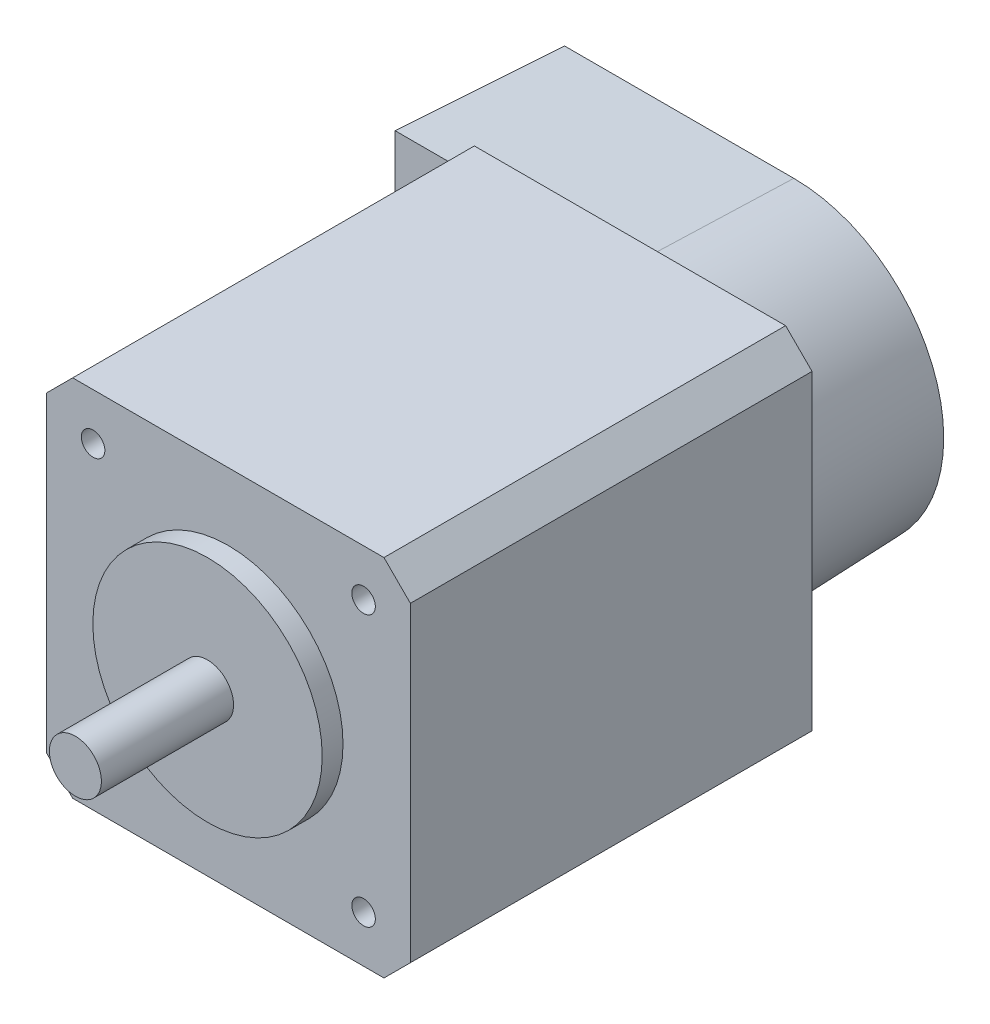
SolidWorks part; units mm, degrees
ref_plane "Front Plane" through (0, 0, 0) normal (0, 0, 1) x (1, 0, 0)
ref_plane "Top Plane" through (0, 0, 0) normal (0, 1, 0) x (1, 0, 0)
ref_plane "Right Plane" through (0, 0, 0) normal (1, 0, 0) x (0, 0, -1)
sketch "Sketch1" plane through (0, 0, 0) normal (0, 0, 1) x (1, 0, 0)
  line L1 (0, 0) -> (35, 0)
  line L2 (0, 0) -> (0, 35)
  line L3 (0, 35) -> (35, 35)
  line L4 (35, 0) -> (35, 35)
  dimension "D1" = 35
  dimension "D2" = 35
extrude "Boss-Extrude1" add sketch "Sketch1" along normal blind 38.608
chamfer "Chamfer1" distance 2.54 angle 45 4 edges at (0, 0, 19.304) (35, 0, 19.304) (0, 35, 19.304) (35, 35, 19.304)
sketch "Sketch2" plane through (0, 0, 38.608) normal (0, 0, 1) x (1, 0, 0)
  line L0 (1.27, 1.27) -> (33.73, 33.73) construction
  line L1 (0, 2.54) -> (2.54, 0) construction
  line L2 (35, 32.46) -> (32.46, 35) construction
  circle A0 centre (17.5, 17.5) radius 11.0236
  dimension "D1" = 22.0472
extrude "Boss-Extrude2" add sketch "Sketch2" along normal blind 2
sketch "Sketch3" plane through (0, 0, 40.608) normal (0, 0, 1) x (1, 0, 0)
  circle A0 centre (17.5, 17.5) radius 2.5
  dimension "D1" = 5
extrude "Boss-Extrude3" add sketch "Sketch3" along normal blind 12.7
hole_wizard "#4-40 Tapped Hole1" positions "Sketch5" profile "Sketch4" tap size "#4-40" standard "ANSI Inch" end condition through all
sketch "Sketch5" plane through (0, 0, 38.608) normal (0, 0, 1) x (1, 0, 0)
  line L1 (4.5, 30.5) -> (30.5, 30.5)
  line L2 (4.5, 30.5) -> (4.5, 4.5)
  line L3 (4.5, 4.5) -> (30.5, 4.5)
  line L4 (30.5, 30.5) -> (30.5, 4.5)
  line L5 (1.27, 1.27) -> (33.73, 33.73) construction
  line L6 (0, 2.54) -> (2.54, 0) construction
  line L7 (35, 32.46) -> (32.46, 35) construction
  circle A0 centre (17.5, 17.5) radius 2.5 construction
  point P1 (4.5, 30.5)
  point P2 (30.5, 4.5)
  point P163 (4.5, 4.5)
  point P164 (30.5, 30.5)
  dimension "D2" = 13
  dimension "D1" = 26
sketch "Sketch4" plane through (4.5, 30.5, 38.608) normal (1, 0, 0) x (0, -1, 0)
  line L0 (0, 0) -> (0, 38.608)
  line L1 (0, 38.608) -> (1.1303, 38.608)
  line L2 (1.1303, 38.608) -> (1.1303, 0)
  line L5 (1.1303, 0) -> (0, 0)
  line L11 (0, -6.35) -> (0, 107.95) construction
  dimension "Thru Tap Drill Dia." = 2.2606
  dimension "Thru Tap Drill Depth" = 38.608
cosmetic thread "Hole Thread1" parameters "D2"=2.8448
cosmetic thread "Hole Thread2" parameters "D2"=2.8448
cosmetic thread "Hole Thread3" parameters "D2"=2.8448
cosmetic thread "Hole Thread4" parameters "D2"=2.8448
sketch "Sketch6" plane through (0, 0, 0) normal (0, 0, -1) x (-1, 0, 0)
  line L0 (5.08, 2.54) -> (-17.5, 2.54)
  line L1 (-17.5, 32.46) -> (5.08, 32.46)
  line L2 (5.08, 32.46) -> (5.08, 2.54)
  line L3 (-32.46, 35) -> (-2.54, 35) construction
  line L4 (-2.54, 0) -> (-32.46, 0) construction
  line L5 (-35, 2.54) -> (-35, 32.46) construction
  line L6 (0, 32.46) -> (0, 2.54) construction
  arc A0 (-17.5, 2.54) -> (-17.5, 32.46) centre (-17.5, 17.5) cw
  point P13 (-24.9173, 17.2848)
  point P14 (-32.1345, 20.9352)
  point P15 (-31.536, 17.5)
  dimension "D1" = 2.54
  dimension "D2" = 2.54
  dimension "D3" = 2.54
  dimension "D4" = 5.08
extrude "Boss-Extrude4" add sketch "Sketch6" along normal blind 15.748 draft 2
